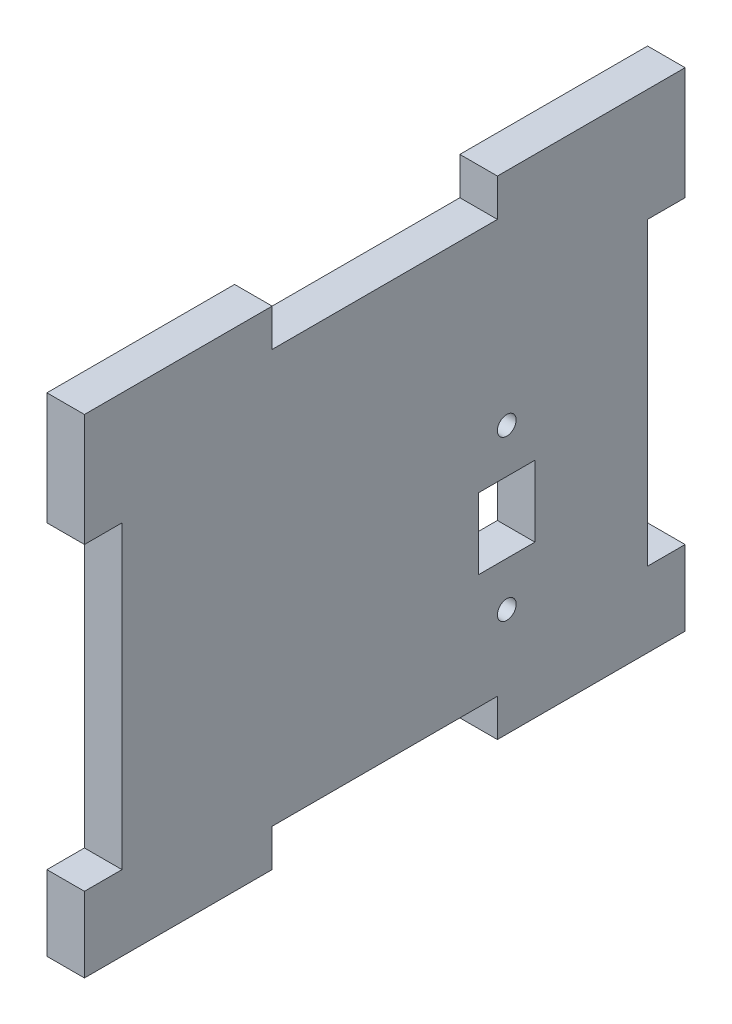
SolidWorks part; units mm, degrees
ref_plane "Front Plane" through (0, 0, 0) normal (0, 0, 1) x (1, 0, 0)
ref_plane "Top Plane" through (0, 0, 0) normal (0, 1, 0) x (1, 0, 0)
ref_plane "Right Plane" through (0, 0, 0) normal (1, 0, 0) x (0, 0, -1)
sketch "Sketch1" plane through (0, 0, 0) normal (1, 0, 0) x (0, 0, -1)
  line L1 (-50.8, -41.275) -> (50.8, -41.275)
  line L2 (-50.8, -41.275) -> (-50.8, 41.275)
  line L3 (-50.8, 41.275) -> (50.8, 41.275)
  line L4 (50.8, -41.275) -> (50.8, 41.275)
  line L5 (-50.8, -41.275) -> (50.8, 41.275) construction
  line L6 (-50.8, 41.275) -> (50.8, -41.275) construction
  line L7 (-19.05, -41.275) -> (19.05, -41.275)
  line L8 (-19.05, -41.275) -> (-19.05, -34.925)
  line L9 (-19.05, -34.925) -> (19.05, -34.925)
  line L10 (19.05, -41.275) -> (19.05, -34.925)
  line L11 (-50.8, -28.575) -> (-44.45, -28.575)
  line L12 (-50.8, -28.575) -> (-50.8, 22.225)
  line L13 (-50.8, 22.225) -> (-44.45, 22.225)
  line L14 (-44.45, -28.575) -> (-44.45, 22.225)
  line L15 (50.8, -28.575) -> (44.45, -28.575)
  line L16 (50.8, -28.575) -> (50.8, 22.225)
  line L17 (50.8, 22.225) -> (44.45, 22.225)
  line L18 (44.45, -28.575) -> (44.45, 22.225)
  line L19 (-19.05, 41.275) -> (19.05, 41.275)
  line L20 (-19.05, 41.275) -> (-19.05, 34.925)
  line L21 (-19.05, 34.925) -> (19.05, 34.925)
  line L22 (19.05, 41.275) -> (19.05, 34.925)
  point P0 (0, 0)
  dimension "D1" = 101.6
  dimension "D2" = 82.55
  dimension "D3" = 6.35
  dimension "D4" = 31.75
  dimension "D5" = 31.75
  dimension "D6" = 6.35
  dimension "D7" = 6.35
  dimension "D8" = 12.7
  dimension "D9" = 19.05
  dimension "D10" = 6.35
extrude "Boss-Extrude1" add sketch "Sketch1" along normal blind 6.35 contours L10 L1 L4 L3 L2 L8 L9
extrude "Cut-Extrude1" cut sketch "Sketch2" against normal blind 6.35
sketch "Sketch2" plane through (6.35, 95.4107, 69.8214) normal (1, 0, 0) x (0, 0, -1)
  line L1 (85.6964, -98.935) -> (95.2214, -98.935)
  line L2 (85.6964, -98.935) -> (85.6964, -110.9365)
  line L3 (85.6964, -110.9365) -> (95.2214, -110.9365)
  line L4 (95.2214, -98.935) -> (95.2214, -110.9365)
  line L5 (85.6964, -98.935) -> (95.2214, -110.9365) construction
  line L6 (85.6964, -110.9365) -> (95.2214, -98.935) construction
  circle A0 centre (90.4589, -118.4295) radius 1.5875
  circle A2 centre (90.4589, -91.442) radius 1.5875
  point P4 (90.4589, -104.9357)
